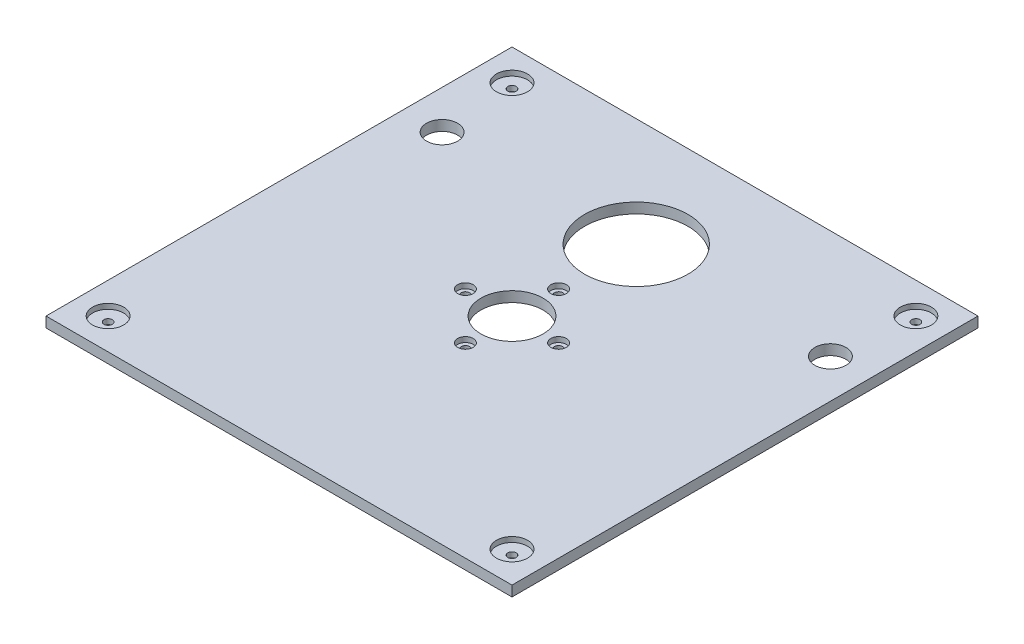
SolidWorks part; units mm, degrees
ref_plane "Alzado" through (0, 0, 0) normal (0, 0, 1) x (1, 0, 0)
ref_plane "Planta" through (0, 0, 0) normal (0, 1, 0) x (1, 0, 0)
ref_plane "Vista lateral" through (0, 0, 0) normal (1, 0, 0) x (0, 0, -1)
sketch "Croquis1" plane through (0, 0, 0) normal (0, 1, 0) x (1, 0, 0)
  line L1 (-225, -225) -> (225, -225)
  line L2 (-225, -225) -> (-225, 225)
  line L3 (-225, 225) -> (225, 225)
  line L4 (225, -225) -> (225, 225)
  line L5 (-225, -225) -> (225, 225) construction
  line L6 (-225, 225) -> (225, -225) construction
  circle A1 centre (0, 0) radius 30
  circle A2 centre (0, 0) radius 120 construction
  circle A3 centre (0, 120) radius 50
  circle A4 centre (-187.5, 120) radius 15
  circle A5 centre (187.5, 120) radius 15
  point P14 (0, 0)
  point P15 (0, 0)
  point P16 (0, 0)
  dimension "D1" = 37.5
  dimension "D2" = 60
  dimension "D3" = 240
  dimension "D4" = 100
  dimension "D6" = 37.5
  dimension "D8" = 30
  dimension "D9" = 30
  dimension "D5" = 450
  dimension "D7" = 105
extrude "Saliente-Extruir1" add sketch "Croquis1" along normal blind 10
sketch "Croquis7" plane through (0, 10, 0) normal (0, 1, 0) x (1, 0, 0)
  circle A0 centre (-195, 195) radius 15
  circle A1 centre (195, 195) radius 15
  circle A2 centre (195, -195) radius 15
  circle A3 centre (-195, -195) radius 15
  circle A4 centre (-45, 0) radius 7.5
  circle A5 centre (0, 45) radius 7.5
  circle A6 centre (0, -45) radius 7.5
  circle A7 centre (45, 0) radius 7.5
  dimension "D1" = 30
  dimension "D2" = 30
  dimension "D3" = 30
  dimension "D4" = 30
  dimension "D5" = 15
  dimension "D6" = 15
  dimension "D7" = 15
  dimension "D8" = 15
  dimension "D9" = 195
  dimension "D10" = 390
  dimension "D11" = 195
  dimension "D12" = 390
  dimension "D13" = 45
  dimension "D14" = 90
  dimension "D15" = 45
  dimension "D16" = 90
extrude "Cortar-Extruir6" cut sketch "Croquis7" against normal blind 5
sketch "Croquis8" plane through (0, 5, 0) normal (0, 1, 0) x (1, 0, 0)
  circle A0 centre (195, -195) radius 4
  circle A1 centre (-195, -195) radius 4
  circle A2 centre (-45, 0) radius 4
  circle A3 centre (45, 0) radius 4
  circle A4 centre (0, -45) radius 4
  circle A5 centre (0, 45) radius 4
  circle A6 centre (195, 195) radius 4
  circle A7 centre (-195, 195) radius 4
  dimension "D1" = 8
  dimension "D2" = 8
  dimension "D3" = 8
  dimension "D4" = 8
  dimension "D5" = 8
  dimension "D6" = 8
  dimension "D7" = 8
  dimension "D8" = 8
extrude "Cortar-Extruir7" cut sketch "Croquis8" against normal blind 5
